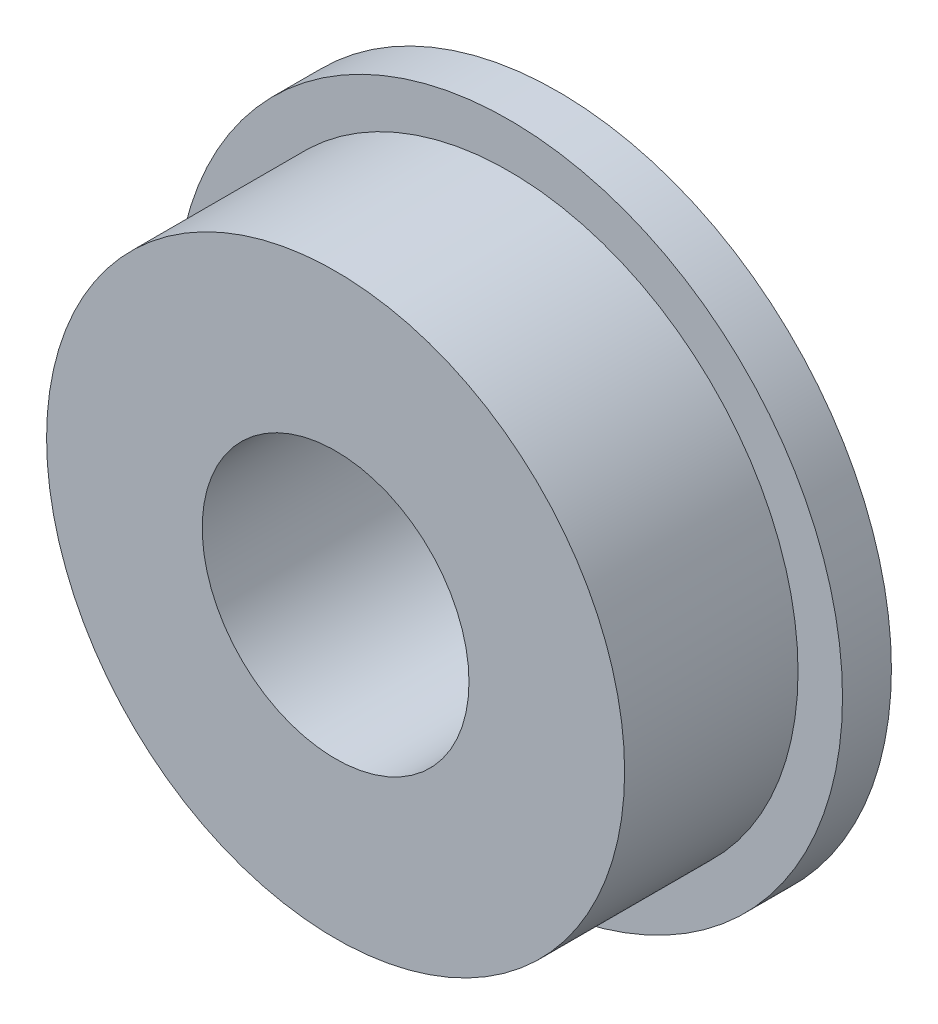
SolidWorks part; units mm, degrees
ref_plane "前视基准面" through (0, 0, 0) normal (0, 0, 1) x (1, 0, 0)
ref_plane "上视基准面" through (0, 0, 0) normal (0, 1, 0) x (1, 0, 0)
ref_plane "右视基准面" through (0, 0, 0) normal (1, 0, 0) x (0, 0, -1)
sketch "草图1" plane through (0, 0, 0) normal (0, 0, 1) x (1, 0, 0)
  circle A0 centre (0, 0) radius 7.5
  circle A1 centre (0, 0) radius 3
  dimension "D1" = 15
  dimension "D2" = 6
extrude "凸台-拉伸1" add sketch "草图1" along normal blind 5
sketch "草图2" plane through (0, 0, 5) normal (0, 0, 1) x (1, 0, 0)
  circle A0 centre (0, 0) radius 6.5
  circle A1 centre (0, 0) radius 7.5 construction
  circle A2 centre (0, 0) radius 7.5
  dimension "D1" = 13
extrude "切除-拉伸1" cut sketch "草图2" against normal blind 3.9
chamfer "倒角1" distance 0.1 angle 50 1 edges at (3, 0, 0)
